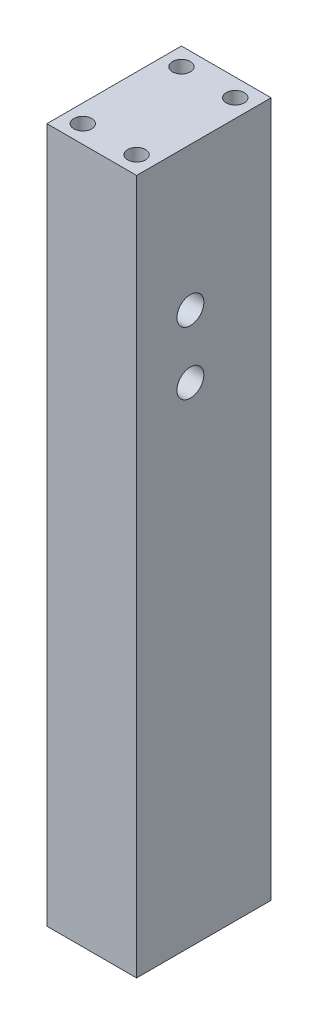
SolidWorks part; units mm, degrees
ref_plane "Front Plane" through (0, 0, 0) normal (0, 0, 1) x (1, 0, 0)
ref_plane "Top Plane" through (0, 0, 0) normal (0, 1, 0) x (1, 0, 0)
ref_plane "Right Plane" through (0, 0, 0) normal (1, 0, 0) x (0, 0, -1)
sketch "Sketch1" plane through (0, 0, 0) normal (1, 0, 0) x (0, 0, -1)
  line L1 (0, 0) -> (15, 0)
  line L2 (0, 0) -> (0, 77.5)
  line L3 (0, 77.5) -> (15, 77.5)
  line L4 (15, 0) -> (15, 77.5)
  dimension "D1" = 77.5
  dimension "D2" = 15
extrude "Boss-Extrude1" add sketch "Sketch1" along normal blind 10
ref_plane "Plane1" through (0, 77.5, 0) normal (0, 1, 0) x (1, 0, 0)
sketch "Sketch3" plane through (0, 77.5, 0) normal (0, 1, 0) x (1, 0, 0)
  line L0 (5, 15) -> (5, 0)
  line L1 (10, 15) -> (0, 15) construction
  line L2 (-5.5, 0) -> (5.5, 0) construction
  line L3 (10, 7.5) -> (0, 7.5)
  line L4 (10, 15) -> (10, 0) construction
  line L5 (0, -8.25) -> (0, 8.25) construction
  circle A0 centre (2, 13) radius 1
  circle A1 centre (8, 13) radius 1
  circle A2 centre (8, 2) radius 1
  circle A3 centre (2, 2) radius 1
  dimension "D1" = 2
  dimension "D2" = 2
  dimension "D3" = 2
extrude "Cut-Extrude1" cut sketch "Sketch3" against normal blind 10 contours A0 | A1 | A2 | A3
ref_plane "Plane2" through (0, 0, 0) normal (0, -1, 0) x (-1, 0, 0)
sketch "Sketch4" plane through (0, 0, 0) normal (0, -1, 0) x (-1, 0, 0)
  line L0 (-5, 15) -> (-5, 0)
  line L1 (-10, 15) -> (0, 15) construction
  line L2 (-5.5, 0) -> (5.5, 0) construction
  line L3 (-10, 7.5) -> (0, 7.5)
  line L4 (-10, 0) -> (-10, 15) construction
  line L5 (0, 8.25) -> (0, -8.25) construction
  circle A0 centre (-2, 2) radius 1
  circle A1 centre (-8, 2) radius 1
  circle A2 centre (-8, 13) radius 1
  circle A3 centre (-2, 13) radius 1
  dimension "D1" = 2
  dimension "D3" = 2
  dimension "D2" = 2
extrude "Cut-Extrude2" cut sketch "Sketch4" against normal blind 10 contours A1 | A2 | A3 | A0
ref_plane "Plane3" through (10, 0, 0) normal (1, 0, 0) x (0, 0, -1)
sketch "Sketch5" plane through (10, 0, 0) normal (1, 0, 0) x (0, 0, -1)
  line L0 (15, 0) -> (15, 77.5) construction
  line L1 (5.5, 77.5) -> (-5.5, 77.5) construction
  line L2 (0, 5.5) -> (0, -5.5) construction
  line L3 (0, 64.75) -> (15, 64.75)
  line L4 (0, 64.75) -> (0, 51.25)
  line L5 (0, 51.25) -> (15, 51.25)
  line L6 (15, 64.75) -> (15, 51.25)
  line L7 (0, 58) -> (15, 58)
  line L8 (7.5, 64.75) -> (7.5, 51.25)
  circle A0 centre (6, 61.5) radius 1.5
  circle A1 centre (6, 54.5) radius 1.5
  dimension "D1" = 3
  dimension "D2" = 6
  dimension "D3" = 16
  dimension "D4" = 13.5
  dimension "D5" = 12.75
extrude "Cut-Extrude3" cut sketch "Sketch5" against normal blind 5 contours A0 | A1
